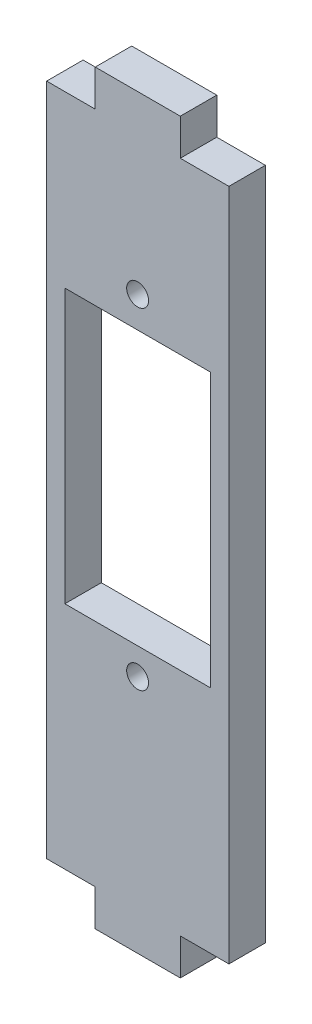
SolidWorks part; units mm, degrees
ref_plane "Front Plane" through (0, 0, 0) normal (0, 0, 1) x (1, 0, 0)
ref_plane "Top Plane" through (0, 0, 0) normal (0, 1, 0) x (1, 0, 0)
ref_plane "Right Plane" through (0, 0, 0) normal (1, 0, 0) x (0, 0, -1)
sketch "Sketch1" plane through (0, 0, 0) normal (0, 0, 1) x (1, 0, 0)
  line L1 (-7.5, 30.71) -> (7.5, 30.71)
  line L2 (-7.5, 30.71) -> (-7.5, -30.71)
  line L3 (-7.5, -30.71) -> (7.5, -30.71)
  line L4 (7.5, 30.71) -> (7.5, -30.71)
  line L5 (-7.5, 30.71) -> (7.5, -30.71) construction
  line L6 (-7.5, -30.71) -> (7.5, 30.71) construction
  point P0 (0, 0)
  dimension "D1" = 61.42
  dimension "D2" = 15
extrude "Boss-Extrude2" add sketch "Sketch1" along normal blind 3
sketch "Sketch4" plane through (0, 0, 3) normal (0, 0, 1) x (1, 0, 0)
  line L1 (-7.5, 30.71) -> (-3.5, 30.71)
  line L2 (-7.5, 30.71) -> (-7.5, 27.71)
  line L3 (-7.5, 27.71) -> (-3.5, 27.71)
  line L4 (-3.5, 30.71) -> (-3.5, 27.71)
  dimension "D1" = 3
  dimension "D2" = 4
extrude "Cut-Extrude2" cut sketch "Sketch4" against normal blind 3
mirror "Mirror1" about plane through (0, 0, 0) normal (1, 0, 0) of "Cut-Extrude2"
mirror "Mirror2" about plane through (0, 0, 0) normal (0, 1, 0) of "Mirror1", "Cut-Extrude2"
sketch "Sketch5" plane through (0, 0, 3) normal (0, 0, 1) x (1, 0, 0)
  line L0 (3.5, 30.71) -> (-3.5, 30.71) construction
  line L1 (-6, 13.71) -> (6, 13.71)
  line L2 (-6, 13.71) -> (-6, -8.79)
  line L3 (-6, -8.79) -> (6, -8.79)
  line L4 (6, 13.71) -> (6, -8.79)
  point P6 (0, 13.71)
  point P7 (0, 30.71)
  dimension "D1" = 22.5
  dimension "D3" = 12
  dimension "D4" = 17
extrude "Cut-Extrude3" cut sketch "Sketch5" against normal blind 3
sketch "Sketch7" plane through (0, 0, 0) normal (0, 0, -1) x (-1, 0, 0)
  line L0 (7.5, 27.71) -> (7.5, -27.71) construction
  line L1 (3.5, -30.71) -> (-3.5, -30.71) construction
  line L2 (-3.5, 30.71) -> (3.5, 30.71) construction
  circle A0 centre (0.0129, 16.255) radius 0.9
  circle A1 centre (0.0129, -10.995) radius 0.9
  point P4 (0, 0)
  dimension "D1" = 1.8
  dimension "D2" = 1.8
  dimension "D3" = 7.4871
  dimension "D4" = 19.715
  dimension "D5" = 7.4871
  dimension "D6" = 14.455
extrude "Cut-Extrude4" cut sketch "Sketch7" against normal through all
